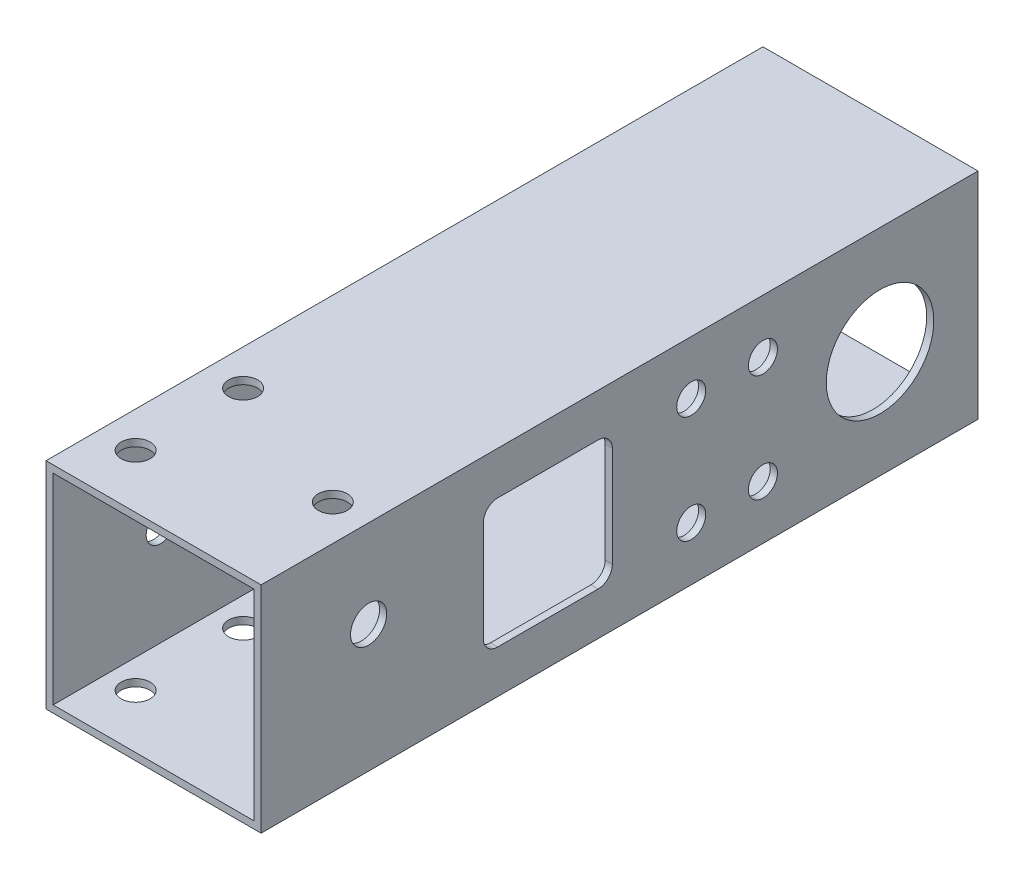
SolidWorks part; units mm, degrees
material "6063-T5"
ref_plane "前视基准面" through (0, 0, 0) normal (0, 0, 1) x (1, 0, 0)
ref_plane "上视基准面" through (0, 0, 0) normal (0, 1, 0) x (1, 0, 0)
ref_plane "右视基准面" through (0, 0, 0) normal (1, 0, 0) x (0, 0, -1)
other "Configuration Table"
sketch "草图1" plane through (0, 0, 0) normal (0, 0, 1) x (1, 0, 0)
  line L1 (-15, -15) -> (15, -15)
  line L2 (-15, -15) -> (-15, 15)
  line L3 (-15, 15) -> (15, 15)
  line L4 (15, -15) -> (15, 15)
  line L5 (-15, -15) -> (15, 15) construction
  line L6 (-15, 15) -> (15, -15) construction
  point P0 (0, 0)
  dimension "D1" = 30
extrude "凸台-拉伸1" add sketch "草图1" along normal mid plane 100
sketch "草图2" plane through (0, 0, 50) normal (0, 0, 1) x (1, 0, 0)
  line L12 (14, -14) -> (14, 14)
  line L13 (14, 14) -> (-14, 14)
  line L14 (-14, 14) -> (-14, -14)
  line L15 (-14, -14) -> (14, -14)
  line L16 (14, -14) -> (14, 14)
  line L17 (14, 14) -> (-14, 14)
  line L18 (-14, 14) -> (-14, -14)
  line L19 (-14, -14) -> (14, -14)
  dimension "D1" = 1
extrude "切除-拉伸1" cut sketch "草图2" against normal through all both and the other way through all
sketch "草图3" plane through (-15, 0, 0) normal (-1, 0, 0) x (0, 0, 1)
  circle A0 centre (10, 0) radius 2.025
  circle A1 centre (35, 0) radius 2.025
  dimension "D1" = 4.05
extrude "切除-拉伸2" cut sketch "草图3" against normal up to surface (1 mm away) up to face at (-14, 0, 0)
sketch "草图4" plane through (14, 0, 0) normal (-1, 0, 0) x (0, 0, 1)
  line L0 (50, 15) -> (-50, 15) construction
  line L1 (26, -9) -> (44, -9) construction
  line L2 (26, -9) -> (26, 9) construction
  line L3 (26, 9) -> (44, 9) construction
  line L4 (44, -9) -> (44, 9) construction
  line L5 (26, -9) -> (44, 9) construction
  line L6 (26, 9) -> (44, -9) construction
  line L7 (1, -9) -> (19, -9)
  line L8 (1, -9) -> (1, 9)
  line L9 (1, 9) -> (19, 9)
  line L10 (19, -9) -> (19, 9)
  line L11 (1, -9) -> (19, 9) construction
  line L12 (1, 9) -> (19, -9) construction
  point P0 (35, 0)
  point P6 (10, 0)
  dimension "D1" = 6
  dimension "D2" = 18
extrude "切除-拉伸3" cut sketch "草图4" against normal up to surface (1 mm away) up to face at (15, 0, 0)
fillet "圆角1" radius 2 4 edges at (14.5, -9, 1) (14.5, 9, 19) (14.5, -9, 19) (14.5, 9, 1)
sketch "草图5" plane through (0, -14, 0) normal (0, 1, 0) x (1, 0, 0)
  line L4 (15, 50) -> (-15, 50)
  line L5 (-15, 50) -> (-15, -50)
  line L6 (-15, -50) -> (15, -50)
  line L7 (15, -50) -> (15, 50)
  line L8 (15, 50) -> (-15, 50)
  line L9 (-15, 50) -> (-15, -50)
  line L10 (-15, -50) -> (15, -50)
  line L11 (15, -50) -> (15, 50)
  circle A0 centre (-10, -42.5) radius 2.025
  circle A1 centre (-10, -27.5) radius 2.025
  dimension "D2" = 4.05
  dimension "D3" = 15
  dimension "D4" = 7.5
  dimension "D5" = 5
  dimension "D1" = 0
extrude "切除-拉伸5" cut sketch "草图5" against normal through all both and the other way through all contours A1 | A0
mirror "镜向1" about plane through (0, 0, 0) normal (1, 0, 0) of "切除-拉伸5"
sketch "草图6" plane through (-15, 0, 0) normal (-1, 0, 0) x (0, 0, 1)
  line L0 (50, 15) -> (-50, 15) construction
  line L1 (50, 15) -> (50, -15) construction
  circle A0 centre (35, 0) radius 2.025
  circle A1 centre (-20, -7.5) radius 2.025
  circle A2 centre (-20, 7.5) radius 2.025
  dimension "D1" = 4.05
  dimension "D2" = 7.5
  dimension "D3" = 15
  dimension "D4" = 70
  dimension "D5" = 15
  dimension "D6" = 35
extrude "切除-拉伸6" cut sketch "草图6" against normal through all both and the other way through all
sketch "草图7" plane through (-15, 0, 0) normal (-1, 0, 0) x (0, 0, 1)
  line L0 (50, -15) -> (-50, -15) construction
  line L1 (-50, 15) -> (-50, -15) construction
  circle A0 centre (-36.3415, 0) radius 7.5
  dimension "D1" = 15
  dimension "D3" = 13.6585
  dimension "D2" = 15
extrude "切除-拉伸7" cut sketch "草图7" against normal through all both
sketch "草图8" plane through (-15, 0, 0) normal (-1, 0, 0) x (0, 0, 1)
  line L0 (-20, 7.5) -> (-10, 7.5) construction
  line L1 (-20, -7.5) -> (-10, -7.5) construction
  circle A0 centre (-10, 7.5) radius 2.025
  circle A1 centre (-10, -7.5) radius 2.025
  circle A2 centre (-20, 7.5) radius 2.025 construction
  dimension "D1" = 4.05
  dimension "D2" = 10
extrude "切除-拉伸8" cut sketch "草图8" against normal through all both and the other way through all
sketch "草图9" plane through (0, 15, 0) normal (0, 1, 0) x (1, 0, 0)
  circle A0 centre (10, -27.5) radius 2.25
  circle A1 centre (10, -42.5) radius 2.25
  dimension "D1" = 4.5
extrude "凸台-拉伸2" add sketch "草图9" against normal up to surface (1 mm away) up to face at (10, 14, 29.525)
sketch "草图10" plane through (0, -15, 0) normal (0, -1, 0) x (1, 0, 0)
  circle A0 centre (10, 42.5) radius 2.5
  circle A1 centre (10, 27.5) radius 2.5
  dimension "D1" = 5
extrude "凸台-拉伸3" add sketch "草图10" against normal up to surface (1 mm away) up to face at (10, -14, 25.475)
sketch "草图11" plane through (0, 15, 0) normal (0, 1, 0) x (1, 0, 0)
  line L0 (15, -50) -> (15, 50) construction
  line L1 (-10, -27.5) -> (-10, -42.5) construction
  circle A0 centre (10, -35) radius 2.025
  point P8 (-10, -35)
  dimension "D1" = 5
  dimension "D2" = 4.05
extrude "切除-拉伸9" cut sketch "草图11" against normal through all both and the other way through all
sketch "草图12" plane through (15, 0, 0) normal (1, 0, 0) x (0, 0, -1)
  circle A0 centre (-35, 0) radius 2.5
  dimension "D1" = 5
extrude "凸台-拉伸4" add sketch "草图12" against normal up to surface (1 mm away) up to face at (14, 7.5, -12.025)
sketch "草图13" plane through (15, 0, 0) normal (1, 0, 0) x (0, 0, -1)
  line L0 (-50, -15) -> (-50, 15) construction
  line L2 (-50, 15) -> (50, 15) construction
  circle A0 centre (-35, 2.75) radius 2.525 construction
  circle A1 centre (-35, 2.75) radius 2.525
  dimension "D2" = 12.25
  dimension "D3" = 12.25
  dimension "D4" = 5.05
  dimension "D1" = 15
extrude "切除-拉伸10" cut sketch "草图13" against normal up to next
